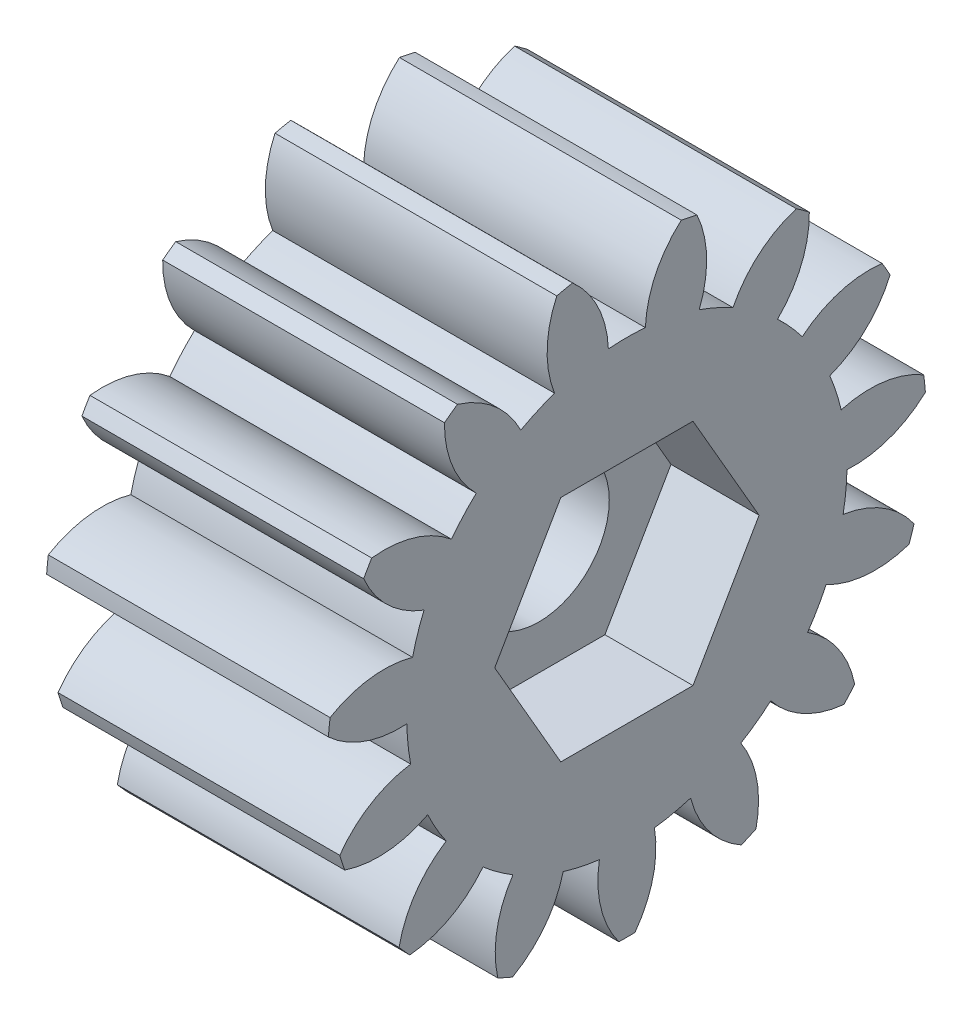
SolidWorks part; units mm, degrees
ref_plane "Plane1" through (0, 0, 0) normal (0, 0, 1) x (1, 0, 0)
ref_plane "Plane2" through (0, 0, 0) normal (0, 1, 0) x (1, 0, 0)
ref_plane "Plane3" through (0, 0, 0) normal (1, 0, 0) x (0, 0, -1)
sketch "HoldingSke" plane through (0, 0, 0) normal (0, 1, 0) x (1, 0, 0)
  line L0 (0, 0) -> (0.483, -0.1294)
  line L1 (-15, 0) -> (100, 0) construction
  line L2 (0, 0) -> (-2.1039, 2.3779)
  line L3 (0, 0) -> (-11.863, 4.5341)
  line L4 (0, 0) -> (8.3417, 2.2352)
  line L5 (0, 0) -> (-46.8476, -17.4728)
  line L6 (0, 0) -> (-13.2634, -8.9489)
  line L7 (-2.1039, 2.3779) -> (8.6586, 51.2059)
  line L8 (-76.2, 54.61) -> (-74.8, 54.61)
  line L9 (-71.009, 38.7566) -> (-53.1078, 45.2721)
  line L10 (-76.2, 71.12) -> (104.1128, 71.12)
  line L11 (0, 0) -> (-16, 0)
  line L12 (-76.2, 101.6) -> (-76.133, 101.6)
  line L13 (24.9733, 27.94) -> (52.9518, 28.4284)
  line L14 (24.9733, 27.94) -> (24.9743, 27.94)
  line L15 (24.9733, 27.94) -> (100.4006, 29.5858)
  line L16 (-63.627, -2) -> (-12.827, -2)
  circle A0 centre (0, 0) radius 4
  circle A1 centre (0, 0) radius 12.499
  circle A2 centre (0, 0) radius 37.5
  circle A3 centre (0, 0) radius 4
  dimension "MHD" = 24.998
  dimension "Hub_dia" = 75
  dimension "Bore" = 8
  dimension "MBD" = 8
  dimension "Num_teeth" = 15
  dimension "Pitch_radius" = 180.3128
  dimension "Pitch" = 0.5
  dimension "Width" = 16
  dimension "Overall_len" = 50
  dimension "Show_teeth" = 15
  dimension "Thickness" = 16
  dimension "OAL" = 50.0001
  dimension "T_dim" = 1.4
  dimension "Ap" = 20
  dimension "H" = 19.05
  dimension "Backlash" = 0.067
  dimension "Addendum_fac" = 1
  dimension "Dedendum_fac" = 1.25
  dimension "Clearance_fac" = 0.25
  dimension "Dedendum_add" = 0.001
  dimension "Module" = 2
sketch "BasProSke" plane through (0, 0, 0) normal (0, 1, 0) x (1, 0, 0)
  line L0 (-10, 0) -> (60, 0) construction
  line L1 (0, 0) -> (0, 17)
  line L2 (0, 0) -> (16, 0)
  line L3 (16, 0) -> (16, 17)
  line L4 (16, 17) -> (0, 17)
  dimension "Diameter" = 34
  dimension "Thickness" = 16
revolve "Base-Revolve" add sketch "BasProSke" angle 360 about L0
sketch "TooCutSke" plane through (0, 0, 0) normal (1, 0, 0) x (0, 0, -1)
  line L1 (0, 0) -> (0, 107) construction
  line L2 (0, 0) -> (-1.6851, 14.905) construction
  line L3 (0, 0) -> (-6.2081, 29.2069) construction
  line L4 (-1.6851, 14.905) -> (-3.1041, 14.6034) construction
  arc A0 (1.0501, 12.4548) -> (-1.0501, 12.4548) centre (0, 0) ccw
  arc A1 (3.1109, 16.7388) -> (-3.1109, 16.7388) centre (0, 0) ccw
  circle A2 centre (0, 0) radius 15 construction
  circle A3 centre (0, 0) radius 14.0954 construction
  arc A4 (-1.0501, 12.4548) -> (-3.1109, 16.7388) centre (-7.045, 12.2085) ccw
  arc A5 (3.1109, 16.7388) -> (1.0501, 12.4548) centre (7.045, 12.2085) ccw
  dimension "Root_dia" = 24.998
  dimension "Overcut_dia" = 34.0508
  dimension "Pitch_dia" = 30
  dimension "Base_dia" = 28.1908
  dimension "Flank_rad" = 6
  dimension "Half_ang" = 12
  dimension "Half_CT" = 1.4507
extrude "ToothCut" cut sketch "TooCutSke" along normal through all
fillet "Breaks" [suppressed] radius 0.04
fillet "RootFillets" [suppressed] radius 0.501
pattern_circular "TeethCuts" count 15 every 24 about axis through (-10, 0, 0) along (1, 0, 0) of "ToothCut", "RootFillets", "Breaks"
sketch "HubNeaOneSke" plane through (0, 0, 0) normal (-1, 0, 0) x (0, 0, 1)
  circle A0 centre (0, 0) radius 12.499
  dimension "Diameter" = 24.998
extrude "HubNearOne" [suppressed] add sketch "HubNeaOneSke" along normal blind 34.0001
sketch "HubNeaBotSke" plane through (0, 0, 0) normal (-1, 0, 0) x (0, 0, 1)
  circle A0 centre (0, 0) radius 12.499
  dimension "Diameter" = 24.998
extrude "HubNearBoth" [suppressed] add sketch "HubNeaBotSke" along normal blind 17
ref_plane "FarPln" through (16, 0, 0) normal (1, 0, 0) x (0, 0, -1)
sketch "HubFarSke" plane through (16, 0, 0) normal (1, 0, 0) x (0, 0, -1)
  circle A0 centre (0, 0) radius 12.499
  dimension "Diameter" = 24.998
extrude "HubFar" [suppressed] add sketch "HubFarSke" along normal blind 17
sketch "BorSke" plane through (0, 0, 0) normal (1, 0, 0) x (0, 0, -1)
  circle A0 centre (0, 0) radius 4
  dimension "Diameter" = 8
extrude "Bore" cut sketch "BorSke" along normal mid plane 100.0001
sketch "KeySke" plane through (0, 0, 0) normal (1, 0, 0) x (0, 0, -1)
  line L0 (-1.5, 0) -> (-1.5, 5.4)
  line L1 (-1.5, 5.4) -> (1.5, 5.4)
  line L2 (1.5, 5.4) -> (1.5, 0)
  line L3 (0, 0) -> (0, 34) construction
  line L4 (-1.5, 0) -> (1.5, 0)
  dimension "Offset" = 5.4
  dimension "Width" = 3
extrude "Keyway" [suppressed] cut sketch "KeySke" along normal mid plane 100.0001
pattern_circular "Keyway2" [suppressed] count 2 every 90 about axis through (-10, 0, 0) along (1, 0, 0)
sketch "Sketch1" plane through (16, 0, 0) normal (1, 0, 0) x (0, 0, -1)
  line L1 (-3.7528, 6.5) -> (-7.5056, 0)
  line L2 (-7.5056, 0) -> (-3.7528, -6.5)
  line L3 (-3.7528, -6.5) -> (3.7528, -6.5)
  line L4 (3.7528, -6.5) -> (7.5056, 0)
  line L5 (7.5056, 0) -> (3.7528, 6.5)
  line L6 (3.7528, 6.5) -> (-3.7528, 6.5)
  circle A0 centre (0, 0) radius 6.5 construction
  dimension "D1" = 13
extrude "Cut-Extrude1" cut sketch "Sketch1" against normal blind 5
equation "' \"Module@HoldingSke\" = 6.35"
equation "' \"Num_teeth@HoldingSke\" = 12"
equation "' \"Ap@HoldingSke\" =  20"
equation "' \"Width@HoldingSke\" = 0.5 * 25.4"
equation "' \"Hub_dia@HoldingSke\"= 1 * 25.4"
equation "' \"Overall_len@HoldingSke\" = 1.0 * 25.4"
equation "' \"Bore@HoldingSke\" = 0.75 * 25.4"
equation "' \"T_dim@HoldingSke\" = 0.1 * 25.4"
equation "' \"Width@KeySke\" = 0.25 * 25.4"
equation "' \"Show_teeth@HoldingSke\" = 13"
equation "' \"Backlash@HoldingSke\" = 0.009 * 25.4"
equation "' \"Addendum_fac@HoldingSke\" = 1.0"
equation "' \"Dedendum_fac@HoldingSke\" = 1.25"
equation "' \"Dedendum_add@HoldingSke\" = 0.00005 * 25.4"
equation "' \"Clearance_fac@HoldingSke\" = 0.25"
equation "\"Pitch@HoldingSke\" = 1 / \"Module@HoldingSke\""
equation "\"Overcut_dia@TooCutSke\" = (\"Num_teeth@HoldingSke\" + 2 * \"Addendum_fac@HoldingSke\") / \"Pitch@HoldingSke\" + 0.002 * 25.4"
equation "\"Pitch_dia@TooCutSke\" = \"Num_teeth@HoldingSke\" / \"Pitch@HoldingSke\""
equation "\"Base_dia@TooCutSke\" = \"Num_teeth@HoldingSke\" / \"Pitch@HoldingSke\" * cos((\"Ap@HoldingSke\"  * 3.14159265 / 180))"
equation "\"Root_dia@TooCutSke\" = (\"Num_teeth@HoldingSke\" + 2) / \"Pitch@HoldingSke\" - 2 * (\"Addendum_fac@HoldingSke\" + \"Dedendum_fac@HoldingSke\") / \"Pitch@HoldingSke\" - \"Dedendum_add@HoldingSke\" * 2"
equation "\"Half_ang@TooCutSke\" = 180 / \"Num_teeth@HoldingSke\""
equation "\"Half_CT@TooCutSke\" = \"Num_teeth@HoldingSke\" / \"Pitch@HoldingSke\" * sin((3.14159265 / 2 / \"Num_teeth@HoldingSke\")) / 2 - 7 * \"Backlash@HoldingSke\" / 4"
equation "\"Flank_rad@TooCutSke\" = \"Num_teeth@HoldingSke\" / \"Pitch@HoldingSke\" / 5"
equation "\"Radius@RootFillets\" = \"Clearance_fac@HoldingSke\" / \"Pitch@HoldingSke\" + \"Dedendum_add@HoldingSke\""
equation "\"Break_rad@Breaks\" = 0.02 / \"Pitch@HoldingSke\""
equation "\"Thickness@HoldingSke\" = \"Width@HoldingSke\""
equation "\"OAL@HoldingSke\" = \"Thickness@HoldingSke\""
equation "\"MHD@HoldingSke\" = (\"Num_teeth@HoldingSke\" + 2) / \"Pitch@HoldingSke\" - 2 * (\"Addendum_fac@HoldingSke\" + \"Dedendum_fac@HoldingSke\")  / \"Pitch@HoldingSke\" - \"Dedendum_add@HoldingSke\" * 2"
equation "\"MBD@HoldingSke\" = (\"Num_teeth@HoldingSke\" + 2) / \"Pitch@HoldingSke\" - 2 * (\"Addendum_fac@HoldingSke\" + \"Dedendum_fac@HoldingSke\")  / \"Pitch@HoldingSke\" - \"Dedendum_add@HoldingSke\" * 2 - 0.002 * 25.4"
equation "\"MHD@HoldingSke\" = ((sgn( \"MHD@HoldingSke\" - \"Hub_dia@HoldingSke\" )-1)*( \"MHD@HoldingSke\" - \"Hub_dia@HoldingSke\" ))/-2+ \"Hub_dia@HoldingSke\""
equation "\"MBD@HoldingSke\" = ((sgn( \"MBD@HoldingSke\" - \"Bore@HoldingSke\" )-1)*( \"MBD@HoldingSke\" - \"Bore@HoldingSke\" ))/-2+ \"Bore@HoldingSke\""
equation "\"OAL@HoldingSke\" = ((sgn( \"OAL@HoldingSke\" - \"Overall_len@HoldingSke\" )+1)*( \"OAL@HoldingSke\" - \"Overall_len@HoldingSke\" ))/2 + \"Overall_len@HoldingSke\" + 0.000002 * 25.4"
equation "\"Num_teeth@TeethCuts\" = int( \"Show_teeth@HoldingSke\" ) + 1"
equation "\"Num_teeth@TeethCuts\" = ((sgn( \"Num_teeth@TeethCuts\" - \"Num_teeth@HoldingSke\" )-1)*( \"Num_teeth@TeethCuts\" - \"Num_teeth@HoldingSke\" ))/-2+ \"Num_teeth@HoldingSke\""
equation "\"Num_teeth@TeethCuts\" = ((sgn( \"Num_teeth@TeethCuts\" - 2.0)+1)*( \"Num_teeth@TeethCuts\" - 2.0))/2 +2.0"
equation "\"Angle@TeethCuts\" = 360.0 / \"Num_teeth@HoldingSke\""
equation "\"Diameter@BasProSke\" = (\"Num_teeth@HoldingSke\" + 2 * \"Addendum_fac@HoldingSke\") / \"Pitch@HoldingSke\""
equation "\"Thickness@BasProSke\"  = \"Thickness@HoldingSke\""
equation "' \"Fillet_rad@BasProSke\" =  \"Thickness@HoldingSke\" * 0.05"
equation "\"MHD@HoldingSke\" = ((sgn( \"MHD@HoldingSke\" - \"Root_dia@TooCutSke\" )-1)*( \"MHD@HoldingSke\" - \"Root_dia@TooCutSke\" ))/-2+ \"Root_dia@TooCutSke\""
equation "\"Diameter@HubNeaOneSke\" = \"MHD@HoldingSke\""
equation "\"Length@HubNearOne\" = \"OAL@HoldingSke\" - \"Thickness@BasProSke\""
equation "\"Diameter@HubNeaBotSke\" = \"MHD@HoldingSke\""
equation "\"Length@HubNearBoth\" = ( \"OAL@HoldingSke\" - \"Thickness@BasProSke\" ) / 2.0"
equation "\"Thickness@FarPln\" = \"Thickness@BasProSke\""
equation "\"Diameter@HubFarSke\" = \"MHD@HoldingSke\""
equation "\"Length@HubFar\" = ( \"OAL@HoldingSke\" - \"Thickness@BasProSke\" ) / 2.0"
equation "\"Diameter@BorSke\" = \"MBD@HoldingSke\""
equation "\"D1@Bore\" = \"OAL@HoldingSke\" * 2.0"
equation "\"D1@Keyway\" = \"OAL@HoldingSke\" * 2.0"
equation "\"Offset@KeySke\" = \"T_dim@HoldingSke\" + \"MBD@HoldingSke\" / 2.0"
